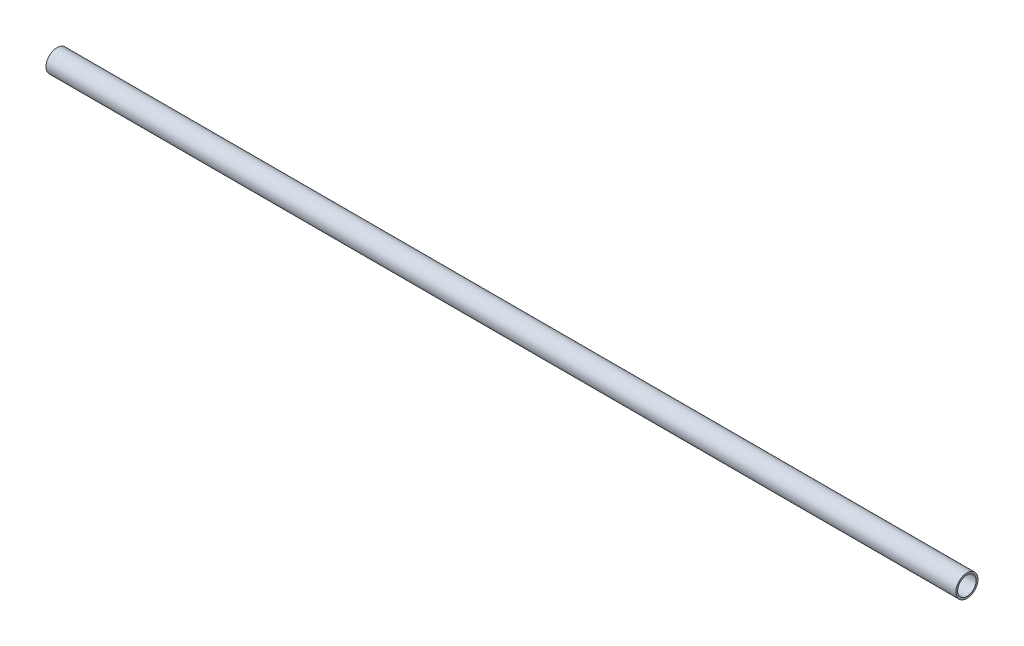
SolidWorks part; units mm, degrees
material "PVC Rigid"
ref_plane "Front Plane" through (0, 0, 0) normal (0, 0, 1) x (1, 0, 0)
ref_plane "Top Plane" through (0, 0, 0) normal (0, 1, 0) x (1, 0, 0)
ref_plane "Right Plane" through (0, 0, 0) normal (1, 0, 0) x (0, 0, -1)
sketch "Sketch1" plane through (0, 0, 0) normal (1, 0, 0) x (0, 0, -1)
  circle A0 centre (0, 0) radius 24.13
  circle A1 centre (0, 0) radius 20.193
  dimension "D1" = 48.26
  dimension "D2" = 40.386
extrude "Boss-Extrude1" add sketch "Sketch1" along normal blind 1981.2
